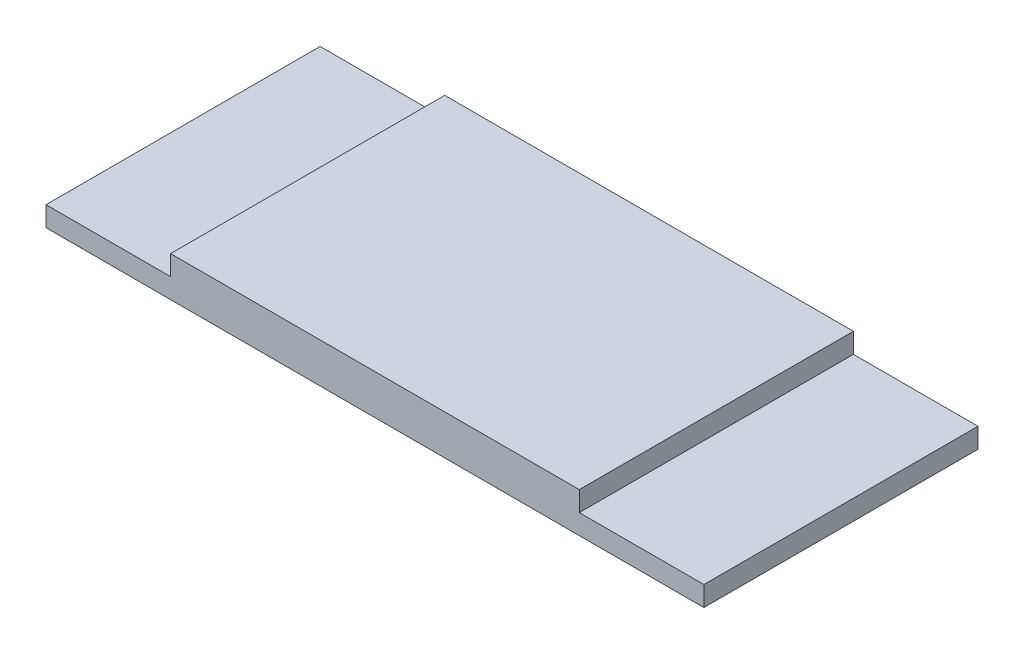
SolidWorks part; units mm, degrees
ref_plane "Спереди" through (0, 0, 0) normal (0, 0, 1) x (1, 0, 0)
ref_plane "Сверху" through (0, 0, 0) normal (0, 1, 0) x (1, 0, 0)
ref_plane "Справа" through (0, 0, 0) normal (1, 0, 0) x (0, 0, -1)
sketch "Эскиз1" plane through (0, 0, 0) normal (0, 1, 0) x (1, 0, 0)
  line L0 (-1000, 0) -> (49000, 0) construction
  line L1 (0, -1000) -> (0, 49000) construction
  line L2 (-8.2, -5.5) -> (8.2, -5.5)
  line L3 (-8.2, 5.5) -> (8.2, 5.5)
  line L4 (8.2, -5.5) -> (8.2, 5.5)
  line L5 (-8.2, -5.5) -> (-8.2, 5.5)
  line L7 (-8.2, -1000) -> (-8.2, 49000) construction
  line L8 (8.2, -1000) -> (8.2, 49000) construction
  line L9 (-1000, 5.5) -> (49000, 5.5) construction
  line L10 (-1000, -5.5) -> (49000, -5.5) construction
  dimension "D1" = 5.5
  dimension "D2" = 5.5
  dimension "D3" = 8.2
  dimension "D4" = 8.2
extrude "Бобышка-Вытянуть1" add sketch "Эскиз1" along normal blind 0.8
sketch "Эскиз3" plane through (0, 0, 0) normal (0, -1, 0) x (1, 0, 0)
  line L0 (-1008.2, 5.5) -> (48991.8, 5.5) construction
  line L1 (-1008.2, -5.5) -> (48991.8, -5.5) construction
  line L2 (-1000, 0) -> (49000, 0) construction
  line L3 (0, -1000) -> (0, 49000) construction
  line L4 (-8.2, -1000.2674) -> (-8.2, 48999.7326) construction
  line L6 (8.2, -1001.0956) -> (8.2, 48998.9044) construction
  line L8 (-13.2, -5.5) -> (-13.2, 5.5)
  line L9 (13.2, -5.5) -> (13.2, 5.5)
  line L10 (-13.2, 5.5) -> (13.2, 5.5)
  line L11 (-13.2, -5.5) -> (13.2, -5.5)
  line L13 (-13.2, -1000.2674) -> (-13.2, 48999.7326) construction
  line L14 (13.2, -1001.0956) -> (13.2, 48998.9044) construction
  dimension "D1" = 5
  dimension "D2" = 5
extrude "Бобышка-Вытянуть2" add sketch "Эскиз3" along normal blind 0.8
